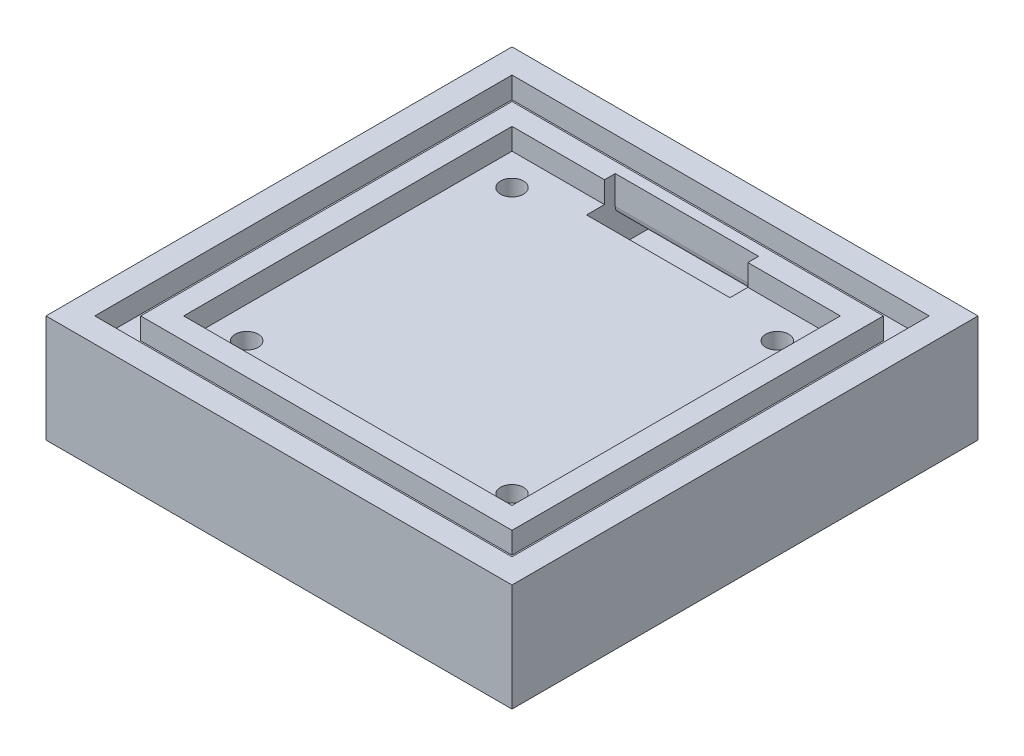
SolidWorks part; units mm, degrees
ref_plane "前视基准面" through (0, 0, 0) normal (0, 0, 1) x (1, 0, 0)
ref_plane "上视基准面" through (0, 0, 0) normal (0, 1, 0) x (1, 0, 0)
ref_plane "右视基准面" through (0, 0, 0) normal (1, 0, 0) x (0, 0, -1)
sketch "草图1" plane through (0, 0, 0) normal (0, 1, 0) x (1, 0, 0)
  line L1 (0, 0) -> (65, 0)
  line L2 (0, 0) -> (0, -65)
  line L3 (0, -65) -> (65, -65)
  line L4 (65, 0) -> (65, -65)
  dimension "D1" = 65
extrude "凸台-拉伸1" add sketch "草图1" along normal blind 15
sketch "草图2" plane through (0, 0, 0) normal (0, -1, 0) x (-1, 0, 0)
  line L0 (-14, -51) -> (-51, -51) construction
  line L1 (-51, -51) -> (-51, -14) construction
  line L2 (-51, -14) -> (-14, -14) construction
  line L3 (-14, -14) -> (-14, -51) construction
  line L4 (-32.5, -14) -> (-32.5, 0) construction
  line L5 (-65, 0) -> (0, 0) construction
  line L6 (-14, -32.5) -> (0, -32.5) construction
  line L7 (0, 0) -> (0, -65) construction
  circle A0 centre (-14, -51) radius 1.6
  circle A1 centre (-51, -51) radius 1.6
  circle A2 centre (-14, -14) radius 1.6
  circle A3 centre (-51, -14) radius 1.6
  dimension "D2" = 3.2
  dimension "D1" = 37
extrude "切除-拉伸1" cut sketch "草图2" against normal through all
sketch "草图3" plane through (0, 15, 0) normal (0, 1, 0) x (1, 0, 0)
  line L0 (32.5, 0) -> (32.5, -9.6) construction
  line L1 (9.6, -9.6) -> (55.4, -9.6)
  line L2 (9.6, -9.6) -> (9.6, -55.4)
  line L3 (9.6, -55.4) -> (55.4, -55.4)
  line L4 (55.4, -9.6) -> (55.4, -55.4)
  line L5 (65, 0) -> (0, 0) construction
  line L6 (9.6, -32.5) -> (0, -32.5) construction
  line L7 (0, 0) -> (0, -65) construction
  dimension "D1" = 45.8
extrude "切除-拉伸2" cut sketch "草图3" against normal blind 3
sketch "草图4" plane through (0, 15, 0) normal (0, 1, 0) x (1, 0, 0)
  line L0 (6.6, -32.5) -> (0, -32.5) construction
  line L1 (58.4, -6.6) -> (6.6, -6.6)
  line L2 (58.4, -6.6) -> (58.4, -58.4)
  line L3 (58.4, -58.4) -> (6.6, -58.4)
  line L4 (6.6, -6.6) -> (6.6, -58.4)
  line L5 (0, 0) -> (0, -65) construction
  line L6 (32.5, -6.6) -> (32.5, 0) construction
  line L7 (65, 0) -> (0, 0) construction
  line L8 (61.6, -3.4) -> (61.6, -61.6)
  line L9 (61.6, -61.6) -> (3.4, -61.6)
  line L10 (3.4, -3.4) -> (3.4, -61.6)
  line L11 (61.6, -3.4) -> (3.4, -3.4)
  dimension "D1" = 51.8
  dimension "D2" = 3.2
extrude "切除-拉伸3" cut sketch "草图4" against normal blind 3
sketch "草图7" plane through (0, 0, 0) normal (0, -1, 0) x (-1, 0, 0)
  circle A0 centre (-14, -14) radius 3
  circle A1 centre (-14, -51) radius 3
  circle A2 centre (-51, -14) radius 3
  circle A3 centre (-51, -51) radius 3
  dimension "D1" = 6
extrude "切除-拉伸6" cut sketch "草图7" against normal blind 5
sketch "草图10" plane through (0, 15, 0) normal (0, 1, 0) x (1, 0, 0)
  line L5 (58.4, -6.6) -> (6.6, -6.6) construction
  line L6 (22.5, -8.1) -> (42.5, -8.1)
  line L7 (22.5, -8.1) -> (22.5, -12.1)
  line L8 (22.5, -12.1) -> (42.5, -12.1)
  line L9 (42.5, -8.1) -> (42.5, -12.1)
  line L10 (42.5, -10.1) -> (55.4, -10.1) construction
  line L11 (55.4, -55.4) -> (55.4, -9.6) construction
  line L12 (22.5, -10.1) -> (9.6, -10.1) construction
  line L13 (9.6, -9.6) -> (9.6, -55.4) construction
  dimension "D1" = 1.5
  dimension "D2" = 4
  dimension "D3" = 20
extrude "切除-拉伸9" cut sketch "草图10" against normal blind 9
sketch "草图11" plane through (0, 0, 0) normal (0, 0, -1) x (-1, 0, 0)
  line L0 (-22.5, 6) -> (-22.5, 15) construction
  line L1 (-42.5, 6) -> (-22.5, 6)
  line L2 (-42.5, 6) -> (-42.5, 10)
  line L3 (-42.5, 10) -> (-22.5, 10)
  line L4 (-22.5, 6) -> (-22.5, 10)
  dimension "D1" = 4
extrude "切除-拉伸10" cut sketch "草图11" against normal blind 9
fillet "圆角2" radius 4 1 edges at (32.5, 6, 12.1)
fillet "圆角3" radius 1 1 edges at (32.5, 10, 8.1)
